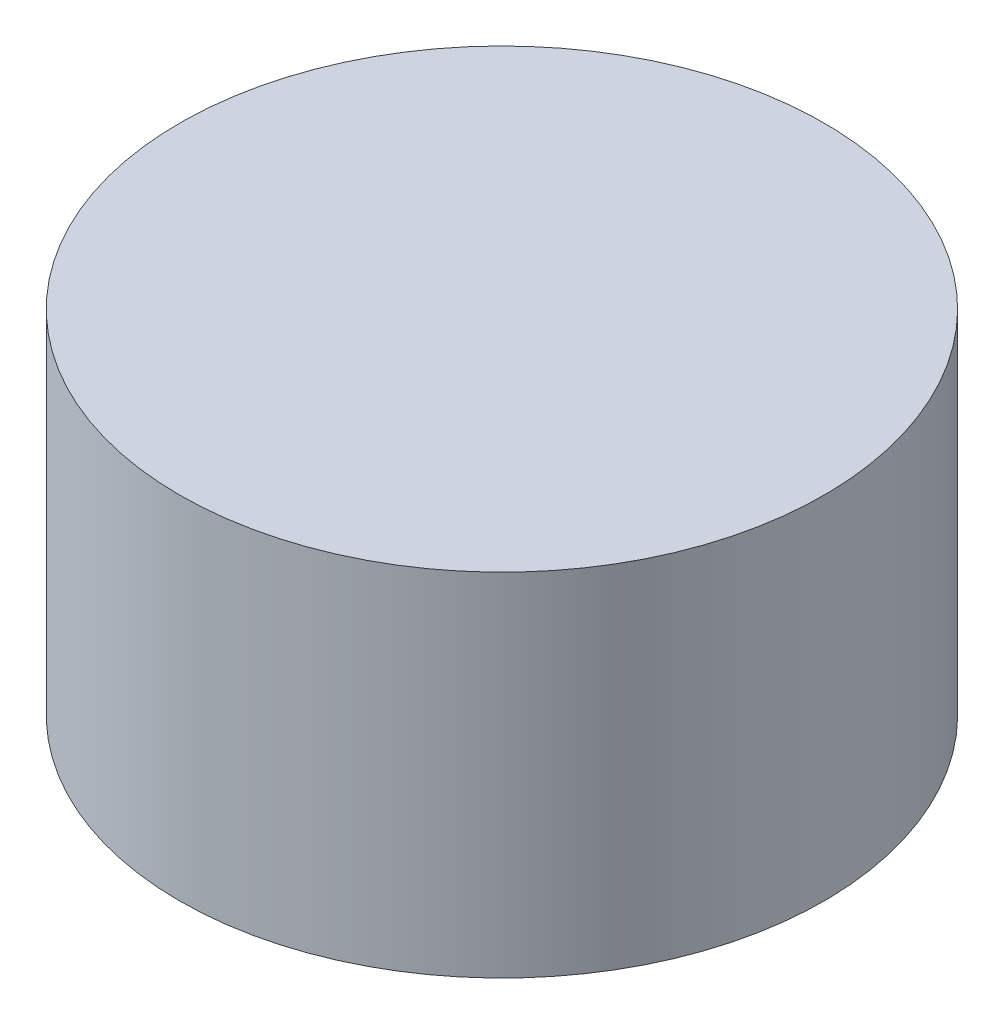
SolidWorks part; units mm, degrees
ref_plane "Front Plane" through (0, 0, 0) normal (0, 0, 1) x (1, 0, 0)
ref_plane "Top Plane" through (0, 0, 0) normal (0, 1, 0) x (1, 0, 0)
ref_plane "Right Plane" through (0, 0, 0) normal (1, 0, 0) x (0, 0, -1)
sketch "Sketch1" plane through (0, 0, 0) normal (0, 1, 0) x (1, 0, 0)
  circle A0 centre (0, 0) radius 8.7312
  dimension "D1" = 17.4625
extrude "Boss-Extrude1" add sketch "Sketch1" along normal blind 9.525
equation "\"0.375n\"=0.125"
